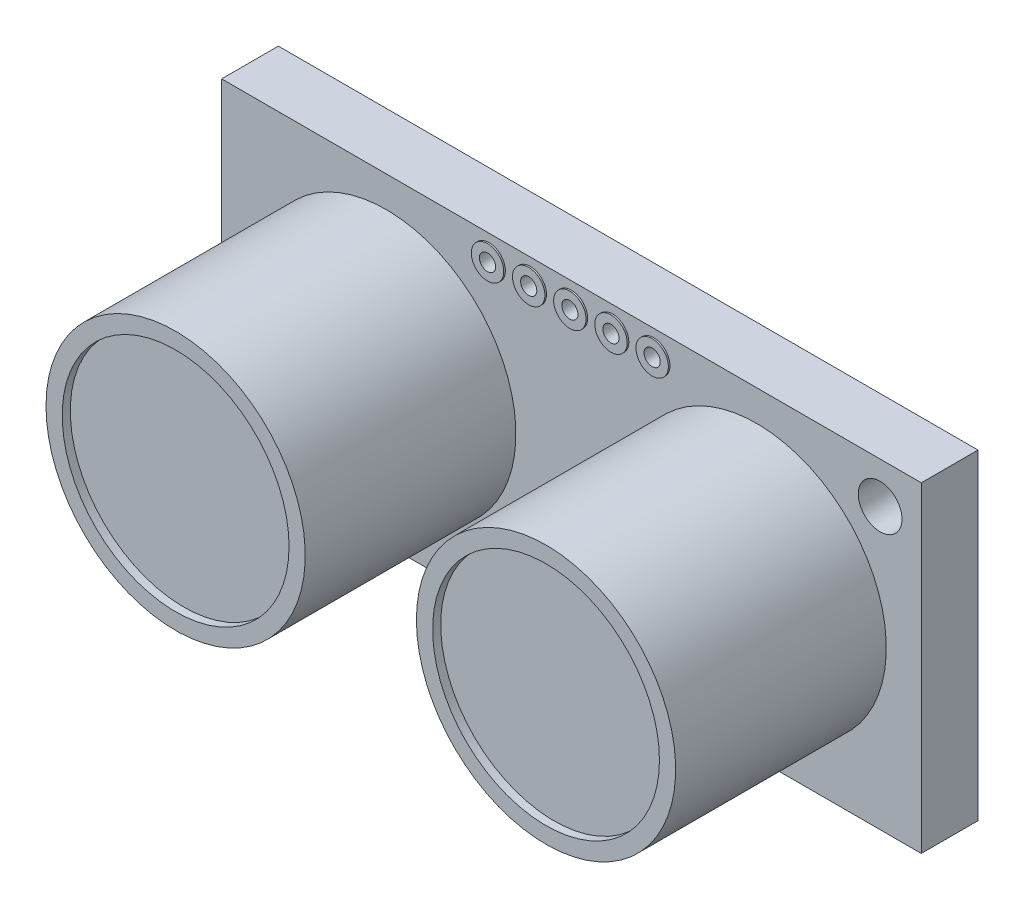
SolidWorks part; units mm, degrees
ref_plane "Front Plane" through (0, 0, 0) normal (0, 0, 1) x (1, 0, 0)
ref_plane "Top Plane" through (0, 0, 0) normal (0, 1, 0) x (1, 0, 0)
ref_plane "Right Plane" through (0, 0, 0) normal (1, 0, 0) x (0, 0, -1)
sketch "Sketch1" plane through (0, 0, 0) normal (0, 0, 1) x (1, 0, 0)
  line L0 (-21.59, 9.906) -> (21.59, 9.906)
  line L1 (-21.59, 9.906) -> (-21.59, -9.906)
  line L2 (-21.59, -9.906) -> (21.59, -9.906)
  line L3 (21.59, 9.906) -> (21.59, -9.906)
  line L4 (0, 9.906) -> (0, -9.906) construction
  line L5 (-21.59, 0) -> (21.59, 0) construction
  circle A2 centre (-19.05, -7.366) radius 1.35
  circle A3 centre (19.05, 7.366) radius 1.35
  point P16 (0, 0)
  point P26 (-21.59, 0)
  point P30 (21.59, 0)
  dimension "D16" = 2.7
  dimension "D4" = 2.54
  dimension "D2" = 2.54
  dimension "D3" = 2.54
  dimension "D5" = 2.54
  dimension "D12" = 43.18
  dimension "D13" = 19.812
other "AlignGroup1"
other "AlignGroup2"
other "AlignGroup3"
other "AlignGroup4"
other "AlignGroup5"
other "AlignGroup6"
extrude "Boss-Extrude1" add sketch "Sketch1" along normal blind 3.5
sketch "Sketch2" plane through (0, 0, 3.5) normal (0, 0, 1) x (1, 0, 0)
  line L1 (-21.59, -9.906) -> (21.59, -9.906) construction
  line L2 (0, -9.906) -> (0, 9.906) construction
  line L3 (21.59, 9.906) -> (-21.59, 9.906) construction
  circle A0 centre (-11.43, 0) radius 8
  circle A1 centre (11.43, 0) radius 8
  dimension "D1" = 7.62
  dimension "D3" = 16
  dimension "D2" = 7.366
extrude "Boss-Extrude2" add sketch "Sketch2" along normal blind 13
sketch "Sketch3" plane through (0, 0, 16.5) normal (0, 0, 1) x (1, 0, 0)
  circle A2 centre (-11.43, 0) radius 7
  circle A3 centre (-11.43, 0) radius 7
  circle A5 centre (11.43, 0) radius 7
  circle A6 centre (11.43, 0) radius 7
  dimension "D1" = 1
  dimension "D2" = 1
extrude "Cut-Extrude1" cut sketch "Sketch3" against normal blind 0.5
sketch "Sketch4" plane through (0, 0, 3.5) normal (0, 0, 1) x (1, 0, 0)
  line L0 (0, 9.906) -> (0, -9.906) construction
  line L1 (21.59, 9.906) -> (-21.59, 9.906) construction
  line L2 (-21.59, -9.906) -> (21.59, -9.906) construction
  line L3 (-21.59, 0) -> (21.59, 0) construction
  line L4 (-21.59, 9.906) -> (-21.59, -9.906) construction
  line L5 (21.59, -9.906) -> (21.59, 9.906) construction
  circle A0 centre (0, 8.406) radius 0.5
  circle A1 centre (2.54, 8.406) radius 0.5
  circle A2 centre (5.08, 8.406) radius 0.5
  circle A3 centre (-5.08, 8.406) radius 0.5
  circle A4 centre (-2.54, 8.406) radius 0.5
  circle A5 centre (-5.08, -8.406) radius 0.5
  circle A6 centre (-2.54, -8.406) radius 0.5
  circle A7 centre (0, -8.406) radius 0.5
  circle A8 centre (2.54, -8.406) radius 0.5
  circle A9 centre (5.08, -8.406) radius 0.5
  dimension "D1" = 1
  dimension "D3" = 2.54
  dimension "D2" = 2.54
  dimension "D4" = 1.5
extrude "Extrude-Thin4" add sketch "Sketch4" along normal blind 0.1 and the other way blind 3.6 thin contours A5 | A6 | A7 | A8 | A9 | A2 | A1 | A0 | A4 | A3
sketch "Sketch11" plane through (0, 0, 3.5) normal (0, 0, 1) x (1, 0, 0)
  circle A0 centre (-5.08, -8.406) radius 0.5
  circle A1 centre (-2.54, -8.406) radius 0.5
  circle A2 centre (0, -8.406) radius 0.5
  circle A3 centre (2.54, -8.406) radius 0.5
  circle A4 centre (5.08, -8.406) radius 0.5
  circle A5 centre (-5.08, 8.406) radius 0.5
  circle A6 centre (-2.54, 8.406) radius 0.5
  circle A7 centre (0, 8.406) radius 0.5
  circle A8 centre (2.54, 8.406) radius 0.5
  circle A9 centre (5.08, 8.406) radius 0.5
extrude "Cut-Extrude2" cut sketch "Sketch11" against normal through all
sketch "Sketch12" plane through (0, 0, 0) normal (0, 0, -1) x (-1, 0, 0)
  line L1 (20.0845, -7.493) -> (20.0845, 7.493) construction
  text T0 "SRF05" font "Arial Rounded MT Bold" height in points 8
extrude "Boss-Extrude3" add sketch "Sketch12" along normal blind 0.001
